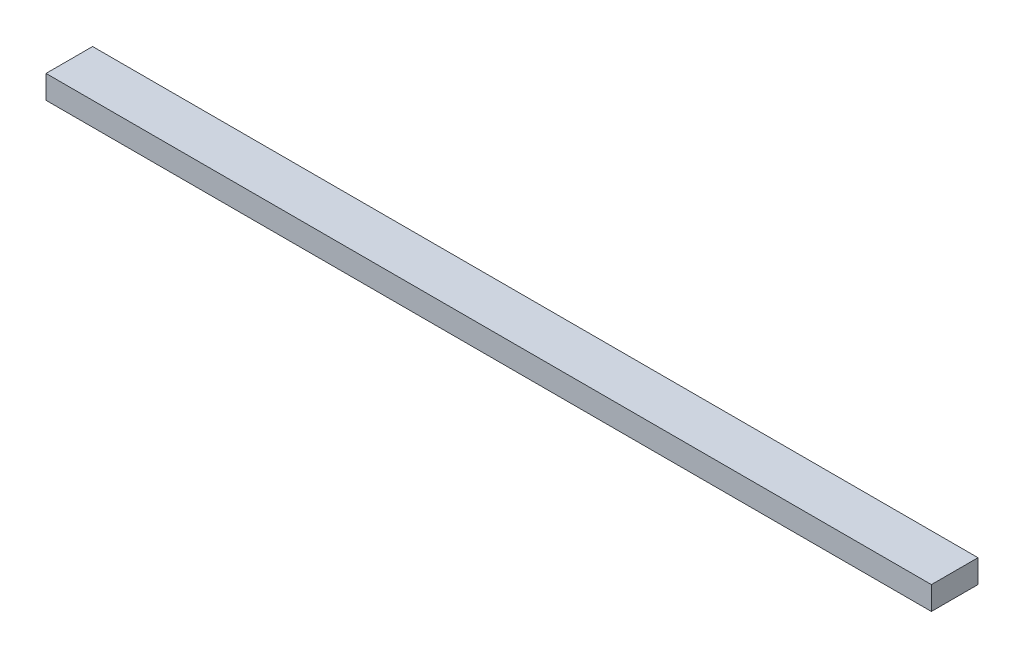
SolidWorks part; units mm, degrees
ref_plane "Front Plane" through (0, 0, 0) normal (0, 0, 1) x (1, 0, 0)
ref_plane "Top Plane" through (0, 0, 0) normal (0, 1, 0) x (1, 0, 0)
ref_plane "Right Plane" through (0, 0, 0) normal (1, 0, 0) x (0, 0, -1)
sketch "Sketch1" plane through (0, 0, 0) normal (0, 1, 0) x (1, 0, 0)
  line L1 (0, 0) -> (-120.65, 0)
  line L2 (0, 0) -> (0, 6.35)
  line L3 (0, 6.35) -> (-120.65, 6.35)
  line L4 (-120.65, 0) -> (-120.65, 6.35)
  dimension "D1" = 120.65
  dimension "D2" = 6.35
extrude "Boss-Extrude1" add sketch "Sketch1" along normal blind 3.175
